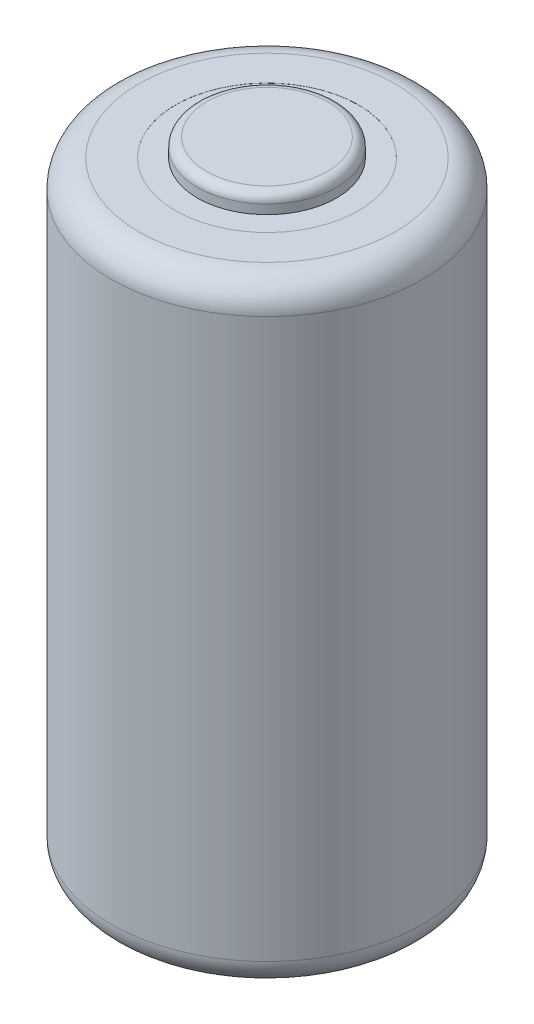
SolidWorks part; units mm, degrees
ref_plane "Ebene vorne" through (0, 0, 0) normal (0, 0, 1) x (1, 0, 0)
ref_plane "Ebene oben" through (0, 0, 0) normal (0, 1, 0) x (1, 0, 0)
ref_plane "Ebene rechts" through (0, 0, 0) normal (1, 0, 0) x (0, 0, -1)
sketch "Skizze1" plane through (0, 0, 0) normal (0, 1, 0) x (1, 0, 0)
  circle A0 centre (0, 0) radius 8.5
  dimension "D1" = 17
extrude "Aufsatz-Linear austragen1" add sketch "Skizze1" along normal blind 33.5
sketch "Skizze2" plane through (0, 33.5, 0) normal (0, 1, 0) x (1, 0, 0)
  circle A0 centre (0, 0) radius 3.8
extrude "Aufsatz-Linear austragen2" add sketch "Skizze2" along normal blind 1
fillet "Verrundung1" radius 1.5 2 edges at (0, 0, 8.5) (0, 33.5, 8.5)
fillet "Verrundung2" radius 0.5 1 edges at (0, 34.5, 3.8)
sketch "Skizze3" plane through (0, 33.5, 0) normal (0, 1, 0) x (1, 0, 0)
  circle A0 centre (0, 0) radius 5
  circle A1 centre (0, 0) radius 3.8
  dimension "D1" = 10
  dimension "D2" = 7.6
extrude "Schnitt-Linear austragen1" cut sketch "Skizze3" against normal blind 0.005
